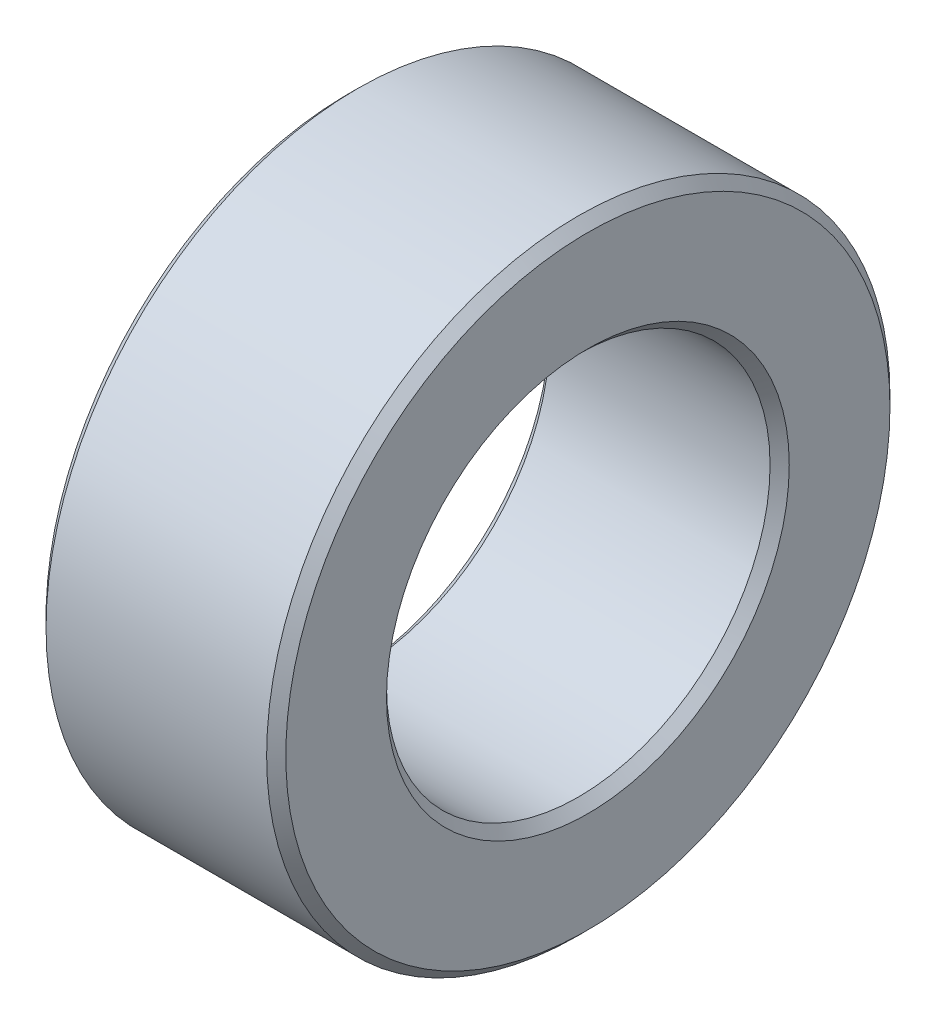
SolidWorks part; units mm, degrees
ref_plane "Front Plane" through (0, 0, 0) normal (0, 0, 1) x (1, 0, 0)
ref_plane "Top Plane" through (0, 0, 0) normal (0, 1, 0) x (1, 0, 0)
ref_plane "Right Plane" through (0, 0, 0) normal (1, 0, 0) x (0, 0, -1)
sketch "Sketch1" plane through (0, 0, 0) normal (1, 0, 0) x (0, 0, -1)
  circle A0 centre (0, 0) radius 6.5
  circle A1 centre (0, 0) radius 4
  dimension "D1" = 13
  dimension "D2" = 8
extrude "Boss-Extrude1" add sketch "Sketch1" along normal blind 5
chamfer "Chamfer1" distance 0.2 angle 45 4 edges at (0, 0, -4) (0, 0, -6.5) (5, 0, -4) (5, 0, -6.5)
